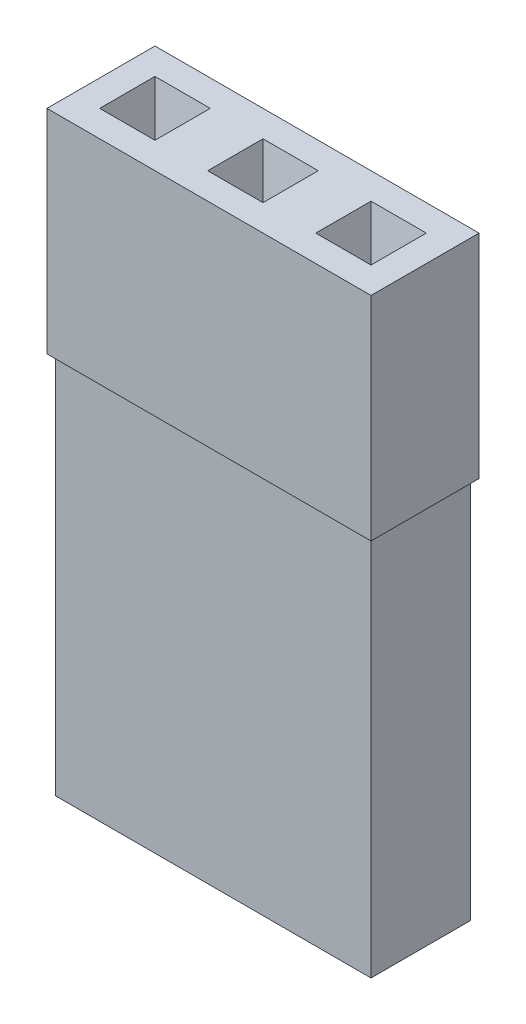
SolidWorks part; units mm, degrees
material "ABS"
ref_plane "Ebene vorne" through (0, 0, 0) normal (0, 0, 1) x (1, 0, 0)
ref_plane "Ebene oben" through (0, 0, 0) normal (0, 1, 0) x (1, 0, 0)
ref_plane "Ebene rechts" through (0, 0, 0) normal (1, 0, 0) x (0, 0, -1)
sketch "Skizze1" plane through (0, 0, 0) normal (0, 1, 0) x (1, 0, 0)
  line L0 (-3.81, 0) -> (3.81, 0) construction
  line L1 (-3.81, -1.27) -> (3.81, -1.27)
  line L2 (-3.81, -1.27) -> (-3.81, 1.27)
  line L3 (-3.81, 1.27) -> (3.81, 1.27)
  line L4 (3.81, -1.27) -> (3.81, 1.27)
  line L5 (-2.19, 0.35) -> (-0.35, 0.35) construction
  line L6 (0.35, 0.35) -> (2.19, 0.35) construction
  line L7 (-2.89, 0.35) -> (-2.19, 0.35)
  line L8 (-2.89, 0.35) -> (-2.89, -0.35)
  line L9 (-2.89, -0.35) -> (-2.19, -0.35)
  line L10 (-2.19, 0.35) -> (-2.19, -0.35)
  line L11 (-0.35, 0.35) -> (0.35, 0.35)
  line L12 (-0.35, 0.35) -> (-0.35, -0.35)
  line L13 (-0.35, -0.35) -> (0.35, -0.35)
  line L14 (0.35, 0.35) -> (0.35, -0.35)
  line L15 (2.19, 0.35) -> (2.89, 0.35)
  line L16 (2.19, 0.35) -> (2.19, -0.35)
  line L17 (2.19, -0.35) -> (2.89, -0.35)
  line L18 (2.89, 0.35) -> (2.89, -0.35)
  line L19 (2.19, -0.35) -> (0.35, -0.35) construction
  line L20 (-0.35, -0.35) -> (-2.19, -0.35) construction
  line L21 (0, 0.35) -> (0, -0.35) construction
  point P0 (0, 0)
  dimension "D1" = 2.54
  dimension "D2" = 7.62
  dimension "D3" = 0.7
  dimension "D4" = 2.54
extrude "Aufsatz-Linear austragen1" add sketch "Skizze1" along normal blind 14
sketch "Skizze3" plane through (0, 0, 0) normal (0, -1, 0) x (1, 0, 0)
  line L8 (3.71, -1.17) -> (3.71, 1.17)
  line L9 (-3.71, -1.17) -> (3.71, -1.17)
  line L10 (-3.71, 1.17) -> (-3.71, -1.17)
  line L11 (3.71, 1.17) -> (-3.71, 1.17)
  line L12 (3.71, -1.17) -> (3.71, 1.17)
  line L13 (-3.71, -1.17) -> (3.71, -1.17)
  line L14 (-3.71, 1.17) -> (-3.71, -1.17)
  line L15 (3.71, 1.17) -> (-3.71, 1.17)
  dimension "D1" = 0.1
extrude "Schnitt-Linear austragen1" cut sketch "Skizze3" against normal blind 9 flip side to cut
chamfer "Fase1" distance 0.3 angle 80 24 edges at (2.54, 0, 0.35) (2.89, 0, 0) (2.54, 0, -0.35) (2.19, 0, 0) (0, 0, -0.35) (0.35, 0, 0) (0, 0, 0.35) (-0.35, 0, 0) (-2.54, 0, -0.35) (-2.19, 0, 0) (-2.54, 0, 0.35) (-2.89, 0, 0) (2.54, 14, 0.35) (2.89, 14, 0) (2.54, 14, -0.35) (2.19, 14, 0) (-0.35, 14, 0) (0, 14, 0.35) (0.35, 14, 0) (0, 14, -0.35) (-2.54, 14, -0.35) (-2.89, 14, 0) (-2.54, 14, 0.35) (-2.19, 14, 0)
